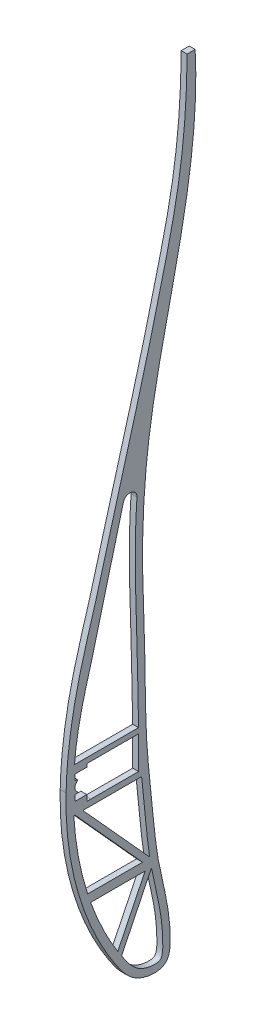
SolidWorks part; units mm, degrees
ref_plane "Front Plane" through (0, 0, 0) normal (0, 0, 1) x (1, 0, 0)
ref_plane "Top Plane" through (0, 0, 0) normal (0, 1, 0) x (1, 0, 0)
ref_plane "Right Plane" through (0, 0, 0) normal (1, 0, 0) x (0, 0, -1)
sketch "rib1" plane through (0, 0, 0) normal (1, 0, 0) x (0, 0, -1)
  line L0 (-71.2313, 530.3957) -> (928.7687, 530.3957) construction
  line L1 (884.1904, 599.9039) -> (887.9745, 599.9039)
  line L2 (856.9345, 370.6416) -> (865.0745, 370.6416)
  line L3 (850.4345, 376.6416) -> (850.4345, 379.6416)
  line L4 (850.4345, 376.6416) -> (850.4345, 373.6416)
  line L5 (840.8063, 376.6416) -> (845.8063, 376.6416) construction
  line L8 (855.8579, 382.6416) -> (843.7452, 382.6416)
  line L9 (855.8579, 382.6416) -> (864.8136, 382.6416)
  line L10 (856.9345, 368.6416) -> (844.7619, 368.6416)
  line L11 (856.9345, 368.6416) -> (865.1127, 368.6416)
  line L12 (866.2204, 340.1291) -> (848.917, 340.1291)
  line L13 (858.3122, 320.8088) -> (858.0269, 320.2668)
  line L14 (848.4203, 343.1291) -> (847.9481, 343.1291)
  line L15 (860.5104, 442.9155) -> (866.5886, 442.9155)
  line L16 (858.0269, 320.2668) -> (873.8862, 320.2668)
  line L17 (855.8579, 318.9992) -> (874.2194, 327.9134) construction
  line L18 (854.766, 321.2482) -> (871.1797, 329.2167) construction
  line L19 (871.1797, 329.2167) -> (873.8862, 320.2668)
  line L20 (843.5049, 367.0528) -> (865.4106, 343.1291)
  line L21 (866.2204, 340.1291) -> (856.8415, 322.3087)
  line L22 (844.7619, 368.6416) -> (867.7752, 343.5082)
  line L23 (868.4574, 340.0851) -> (858.3122, 320.8088)
  line L24 (865.4106, 343.1291) -> (848.4203, 343.1291)
  line L26 (856.9345, 370.6416) -> (850.4345, 370.6416)
  line L27 (850.4345, 370.6416) -> (850.4345, 373.6416)
  line L29 (855.8579, 380.6416) -> (864.9113, 380.6416)
  line L30 (855.8579, 380.6416) -> (850.4345, 380.6416)
  line L31 (850.4345, 380.6416) -> (850.4345, 379.6416)
  circle A0 centre (845.8063, 376.6416) radius 2
  arc A1 (841.0443, 380.5713) -> (847.6718, 415.72) centre (1017.3451, 365.528) cw
  arc A2 (851.2954, 425.5507) -> (861.6081, 456.6454) centre (699.0135, 493.3134) ccw
  arc A3 (862.9829, 461.9026) -> (884.1904, 599.9039) centre (374.0528, 607.6697) ccw
  arc A4 (840.7788, 371.8072) -> (855.8579, 318.9992) centre (950.1899, 374.4922) ccw
  arc A5 (867.6216, 376.9662) -> (872.8022, 332.64) centre (1022.9399, 372.6533) ccw
  arc A6 (867.6216, 376.9662) -> (871.4996, 461.3529) centre (1263.0251, 401.0778) cw
  arc A7 (871.9368, 463.9152) -> (887.9745, 599.9039) centre (-120.6116, 649.9108) ccw
  arc A8 (874.2194, 327.9134) -> (872.8022, 332.64) centre (950.104, 353.2418) cw
  arc A9 (841.0443, 380.5713) -> (840.7788, 371.8072) centre (920.7547, 373.7698) ccw
  arc A10 (851.2954, 425.5507) -> (847.6718, 415.72) centre (924.3857, 393.0268) ccw
  arc A11 (862.9829, 461.9026) -> (861.6081, 456.6454) centre (939.6482, 439.046) ccw
  arc A12 (871.4996, 461.3529) -> (871.9368, 463.9152) centre (950.5681, 449.1804) cw
  arc A13 (843.7452, 382.6416) -> (850.0691, 415.0108) centre (1017.3451, 365.528) cw
  arc A14 (853.5794, 424.5344) -> (850.0691, 415.0108) centre (924.3857, 393.0268) ccw
  arc A15 (853.5794, 424.5344) -> (860.5104, 442.9155) centre (699.0135, 493.3134) ccw
  arc A16 (843.5353, 380.3587) -> (850.0691, 415.0108) centre (1017.3451, 365.528) cw construction
  arc A17 (843.5049, 367.0528) -> (847.9481, 343.1291) centre (950.1899, 374.4922) ccw
  arc A18 (865.0721, 374.4641) -> (865.0745, 370.6416) centre (1022.9399, 372.6533) ccw
  arc A19 (864.962, 379.6766) -> (864.9113, 380.6416) centre (1263.0251, 401.0778) cw
  arc A20 (871.1797, 329.2167) -> (870.3865, 331.9962) centre (950.104, 353.2418) cw
  arc A21 (868.4574, 340.0851) -> (870.3865, 331.9962) centre (1022.9399, 372.6533) ccw
  arc A22 (865.3787, 461.1883) -> (886.6901, 599.8658) centre (374.0528, 607.6697) ccw construction
  arc A23 (865.1195, 376.9245) -> (870.3865, 331.9962) centre (1022.9399, 372.6533) ccw construction
  arc A24 (869.4795, 464.3757) -> (885.4776, 600.0277) centre (-120.6116, 649.9108) ccw construction
  arc A25 (843.278, 371.8685) -> (858.0127, 320.2668) centre (950.1899, 374.4922) ccw construction
  arc A26 (853.5794, 424.5344) -> (864.0469, 456.0955) centre (699.0135, 493.3134) ccw construction
  arc A27 (865.3787, 461.1883) -> (864.0469, 456.0955) centre (939.6482, 439.046) ccw construction
  arc A28 (865.1195, 376.9245) -> (869.0287, 461.7333) centre (1263.0251, 401.0778) cw construction
  arc A29 (869.0287, 461.7333) -> (869.4795, 464.3757) centre (950.5681, 449.1804) cw construction
  arc A30 (848.917, 340.1291) -> (856.8415, 322.3087) centre (950.1899, 374.4922) ccw
  arc A31 (865.1127, 368.6416) -> (867.7752, 343.5082) centre (1022.9399, 372.6533) ccw
  arc A32 (864.8136, 382.6416) -> (866.5886, 442.9155) centre (1263.0251, 401.0778) cw
  arc A33 (865.0721, 374.4641) -> (864.962, 379.6766) centre (785.0773, 375.3817) ccw
  spline S0 degree 3 poles (855.8579, 318.9992) (859.3648, 313.0596) (867.0534, 309.8477) (875.8907, 311.5767) (877.0472, 317.8757) (875.7309, 323.2627) (874.9921, 325.5984) (874.2194, 327.9134) knots 0 0 0 0 0.275026 0.518183 0.708506 0.751927 0.952395 0.952395 0.952395 0.952395
  dimension "D2" = 2.5
  dimension "D1" = 1000
sketch "rib2" plane through (0, 0, 0) normal (1, 0, 0) x (0, 0, -1)
  line L0 (-154.4211, 376.6416) -> (49845.5789, 376.6416) construction
  line L1 (-144.1421, 380.6416) -> (49855.8579, 380.6416) construction
  line L2 (-143.0655, 370.6416) -> (49856.9345, 370.6416) construction
  line L3 (782.8933, 343.3859) -> (760.3563, 368.2109)
  line L4 (-143.0655, 368.6416) -> (49856.9345, 368.6416) construction
  line L5 (-144.1421, 382.6416) -> (49855.8579, 382.6416) construction
  line L6 (785.2354, 343.762) -> (762.6647, 368.6416)
  line L7 (764.6298, 343.3859) -> (782.8933, 343.3859)
  line L8 (783.7374, 340.3859) -> (774.2204, 321.3554)
  line L9 (767.5719, 380.6416) -> (767.5719, 370.6416)
  line L10 (767.5719, 370.6416) -> (782.7291, 370.6416)
  line L11 (767.5719, 380.6416) -> (782.2855, 380.6416)
  line L12 (765.5126, 340.3859) -> (783.7374, 340.3859)
  line L13 (762.6647, 368.6416) -> (782.7755, 368.6416)
  line L14 (776.5435, 321.5294) -> (789.8459, 321.5294)
  line L15 (760.7138, 382.6416) -> (782.1585, 382.6416)
  line L16 (770.7866, 427.4918) -> (781.8144, 427.4918)
  line L17 (801.9062, 590.4081) -> (805.115, 590.4081)
  line L18 (757.9166, 376.6416) -> (762.9166, 376.6416) construction
  line L20 (785.9296, 340.298) -> (776.5435, 321.5294)
  circle A0 centre (762.9166, 376.6416) radius 2
  arc A1 (758.9972, 388.4269) -> (758.7602, 360.0657) centre (857.8646, 373.419) ccw
  spline S0 degree 3 poles (758.7602, 360.0657) (759.4545, 354.9126) (761.6392, 342.918) (767.6025, 326.3565) (776.3644, 313.1833) (785.8807, 308.842) (791.3139, 310.6103) (793.0754, 312.9879) (793.3375, 316.1077) (791.0414, 329.6431) (787.956, 341.1966) (785.2042, 359.6207) (785.4538, 372.9971) (783.4315, 397.4301) (785.2476, 420.7625) (783.0535, 455.8097) (784.4694, 464.3867) (788.1328, 479.2935) (793.2428, 503.9805) (802.5401, 542.6054) (805.2587, 572.3941) (805.115, 590.4081) knots 0.028705 0.028705 0.028705 0.028705 0.059247 0.100348 0.1322 0.149146 0.158796 0.160734 0.16766 0.175847 0.234409 0.24607 0.285136 0.310616 0.385264 0.441942 0.454033 0.506165 0.624061 0.777474 1 1 1 1
  spline S1 degree 3 poles (801.9062, 590.4081) (801.6966, 560.1521) (794.9988, 516.4373) (781.9369, 464.9221) (769.955, 434.3358) (762.9603, 410.299) (759.9193, 394.5015) (758.9972, 388.4269) knots 0 0 0 0 0.408823 0.598513 0.719262 0.854061 0.937351 0.937351 0.937351 0.937351
  spline S2 degree 3 poles (760.3563, 368.2109) (760.6455, 365.1083) (761.2971, 359.3998) (762.6856, 351.2079) (763.8909, 346.0643) (764.604, 343.4789) (764.6298, 343.3859) knots 0.01313 0.01313 0.01313 0.01313 0.031626 0.047245 0.062864 0.063447 0.063447 0.063447 0.063447
  spline S3 degree 3 poles (765.5126, 340.3859) (765.9421, 339.0082) (767.2255, 335.1967) (769.2617, 330.2911) (771.6089, 325.6402) (773.0967, 323.06) (774.0043, 321.6748) (774.2204, 321.3554) knots 0.069751 0.069751 0.069751 0.069751 0.078483 0.094102 0.101912 0.109721 0.112105 0.112105 0.112105 0.112105
  spline S5 degree 3 poles (782.7291, 370.6416) (782.7064, 371.5634) (782.6438, 373.8426) (782.4996, 377.1608) (782.3523, 379.5799) (782.2855, 380.6416) knots 0.276245 0.276245 0.276245 0.276245 0.281529 0.289339 0.295445 0.295445 0.295445 0.295445
  spline S6 degree 3 poles (789.8459, 321.5294) (789.8142, 321.6995) (789.7504, 322.0389) (789.4577, 323.5807) (788.9295, 326.2404) (788.1496, 329.9526) (787.3325, 333.724) (786.5882, 337.1579) (786.1256, 339.3494) (785.9296, 340.298) knots 0.178918 0.178918 0.178918 0.178918 0.179894 0.18087 0.187816 0.195625 0.203435 0.211244 0.21717 0.21717 0.21717 0.21717
  spline S7 degree 3 poles (785.2354, 343.762) (784.9117, 345.4358) (784.3695, 348.4126) (783.6834, 352.846) (783.0923, 358.3507) (782.8866, 363.6197) (782.8011, 367.501) (782.7755, 368.6416) knots 0.224345 0.224345 0.224345 0.224345 0.234672 0.242482 0.250291 0.26591 0.27243 0.27243 0.27243 0.27243
  spline S8 degree 3 poles (782.1585, 382.6416) (782.0098, 384.985) (781.5323, 392.7288) (781.6016, 402.5045) (781.8121, 413.0284) (781.8895, 420.0466) (781.8563, 425.0079) (781.8229, 427.0307) (781.8144, 427.4918) knots 0.299279 0.299279 0.299279 0.299279 0.312767 0.344005 0.359624 0.375243 0.383052 0.385336 0.385336 0.385336 0.385336
  spline S9 degree 3 poles (770.7866, 427.4918) (769.4671, 423.3387) (766.9647, 414.7701) (763.3804, 399.8515) (761.5251, 389.0141) (760.7138, 382.6416) knots 0.752168 0.752168 0.752168 0.752168 0.811773 0.874217 0.962264 0.962264 0.962264 0.962264
  point P26 (765.5126, 340.3859)
  point P30 (764.6298, 343.3859)
  point P35 (774.2204, 321.3554)
  point P36 (789.8459, 321.5294)
  point P37 (785.9296, 340.298)
  point P39 (760.3563, 368.2109)
  point P40 (760.0729, 371.4986)
  dimension "D1" = 100
sketch "Sketch5" plane through (0, 0, 0) normal (1, 0, 0) x (0, 0, -1)
  line L0 (-200154.4211, 376.6416) -> (249845.5789, 376.6416) construction
  line L1 (693.317, 322.1015) -> (707.0464, 322.1015)
  line L2 (695.5696, 447.1101) -> (698.3736, 447.1101)
  line L3 (698.6642, 410.7316) -> (681.8197, 410.7316)
  line L4 (698.7261, 405.5878) -> (680.4847, 405.5878)
  line L5 (677.0801, 382.6416) -> (699.3215, 382.6416)
  line L7 (699.7026, 368.6416) -> (679.4803, 368.6416)
  line L8 (-200143.0655, 368.6416) -> (249856.9345, 368.6416) construction
  line L9 (674.1545, 376.6416) -> (679.1545, 376.6416) construction
  line L10 (684.2181, 380.6416) -> (684.2181, 370.6416)
  line L11 (-200144.1421, 380.6416) -> (249855.8579, 380.6416) construction
  line L12 (-200143.0655, 370.6416) -> (249856.9345, 370.6416) construction
  line L13 (684.2181, 370.6416) -> (699.6248, 370.6416)
  line L14 (702.2048, 368.6416) -> (702.335, 365.9116)
  line L15 (699.3639, 380.6416) -> (684.2181, 380.6416)
  line L16 (708.485, 312.754) -> (708.6651, 312.9152)
  line L17 (706.7921, 314.6987) -> (706.9599, 314.7434)
  line L18 (699.8434, 365.7077) -> (699.7071, 368.5354)
  line L19 (682.1263, 343.4207) -> (681.5591, 343.4207)
  line L20 (700.6109, 340.4181) -> (682.6985, 340.4181)
  line L21 (699.3639, 380.6416) -> (699.6248, 370.6416)
  line L22 (705.0572, 343.4207) -> (704.8181, 343.4207)
  line L23 (716.7384, 582.0418) -> (720.2752, 582.0418)
  line L24 (693.317, 322.1015) -> (702.7962, 340.2834)
  line L25 (702.2445, 343.7103) -> (679.4803, 368.6416)
  line L26 (691.5466, 323.0319) -> (700.6109, 340.4181)
  line L28 (699.8006, 343.4207) -> (682.1263, 343.4207)
  line L32 (699.8006, 343.4207) -> (677.0187, 368.3713)
  circle A0 centre (679.1545, 376.6416) radius 2
  spline S0 degree 3 poles (674.1545, 376.6416) (674.6209, 363.9047) (675.4244, 348.9718) (687.0005, 324.6734) (691.715, 318.3055) (697.5054, 311.9056) (699.9912, 310.5046) (704.8962, 310.5781) (707.1739, 311.6254) (708.485, 312.754) knots 0 0 0 0 0.082297 0.137777 0.177735 0.177735 0.194632 0.194632 0.2043 0.2043 0.2043 0.2043
  spline S1 degree 3 poles (716.7384, 582.0418) (716.9491, 569.6586) (716.384, 531.2528) (699.2016, 484.7456) (692.8166, 441.1757) (677.838, 413.403) (675.0171, 391.1698) (674.1545, 376.6416) knots 0 0 0 0 0.169562 0.555938 0.689283 0.791056 1 1 1 1
  spline S2 degree 3 poles (702.2445, 343.7103) (702.1641, 344.2407) (701.7657, 346.9448) (701.1382, 351.8745) (700.5581, 357.5193) (700.1402, 362.1447) (699.9401, 364.5255) (699.8434, 365.7077) knots 0.317112 0.317112 0.317112 0.317112 0.32289 0.346516 0.370142 0.381955 0.393768 0.393768 0.393768 0.393768
  spline S4 degree 3 poles (702.2048, 368.6416) (701.8669, 376.5926) (701.8555, 384.7425) (701.1266, 402.784) (701.1396, 431.7405) (700.5544, 456.9254) (705.1133, 487.005) (717.5576, 525.1697) (721.078, 562.1394) (720.2752, 582.0418) knots 0.402967 0.402967 0.402967 0.402967 0.483086 0.483086 0.591391 0.687653 0.687653 0.844633 1 1 1 1
  spline S5 degree 3 poles (699.3215, 382.6416) (699.3024, 383.5334) (699.2425, 386.2646) (699.1476, 389.8671) (699.0014, 393.4021) (698.878, 397.2735) (698.7899, 401.3622) (698.7401, 404.5905) (698.7261, 405.5878) knots 0.449941 0.449941 0.449941 0.449941 0.458939 0.477596 0.486925 0.496254 0.514911 0.523067 0.523067 0.523067 0.523067
  spline S6 degree 3 poles (699.7071, 368.5354) (699.7056, 368.5708) (699.7041, 368.6062) (699.7026, 368.6416) knots 0.402967 0.402967 0.402967 0.402967 0.40332 0.40332 0.40332 0.40332
  spline S7 degree 3 poles (682.6985, 340.4181) (683.0121, 339.6321) (683.9949, 337.2558) (685.7648, 333.3639) (687.9735, 329.011) (689.7493, 325.8616) (690.8989, 324.0094) (691.3927, 323.2607) (691.5466, 323.0319) knots 0.095831 0.095831 0.095831 0.095831 0.10215 0.114919 0.127687 0.140456 0.14684 0.149678 0.149678 0.149678 0.149678
  spline S8 degree 3 poles (677.0187, 368.3713) (677.0192, 368.3626) (677.0681, 367.4934) (677.2257, 364.9551) (677.5669, 360.9606) (678.1637, 356.4034) (679.0103, 351.9539) (680.1158, 347.6804) (681.0683, 344.7879) (681.5591, 343.4207) knots 0.019088 0.019088 0.019088 0.019088 0.019153 0.025537 0.038306 0.051075 0.063844 0.076612 0.087747 0.087747 0.087747 0.087747
  spline S9 degree 3 poles (708.6651, 312.9152) (709.0596, 313.2832) (711.3268, 316.9807) (705.4793, 334.2076) (703.6294, 350.0939) (702.335, 365.9116) knots 0.204759 0.204759 0.204759 0.204759 0.207895 0.236848 0.393768 0.393768 0.393768 0.393768
  spline S10 degree 3 poles (676.659, 376.6416) (676.6584, 376.6321) (676.6578, 376.6225) (676.6573, 376.613) knots 0.999862 0.999862 0.999862 0.999862 1 1 1 1
  spline S11 degree 3 poles (707.0464, 322.1015) (707.0052, 322.2371) (706.9227, 322.5094) (706.5342, 323.8003) (705.9077, 326.017) (705.0863, 329.1749) (704.0811, 333.4582) (703.3421, 337.155) (702.8797, 339.7948) (702.7962, 340.2834) knots 0.237993 0.237993 0.237993 0.237993 0.239469 0.240946 0.252011 0.263824 0.275637 0.299263 0.304623 0.304623 0.304623 0.304623
  spline S12 degree 3 poles (680.4847, 405.5878) (680.2388, 404.5378) (679.0822, 399.2686) (677.9122, 391.5905) (677.2696, 384.9533) (677.0801, 382.6416) knots 0.859357 0.859357 0.859357 0.859357 0.875 0.9375 0.970921 0.970921 0.970921 0.970921
  spline S13 degree 3 poles (698.6642, 410.7316) (698.6438, 412.7052) (698.5832, 419.5769) (698.503, 431.741) (698.3426, 441.7088) (698.3711, 446.7739) (698.3736, 447.1101) knots 0.536769 0.536769 0.536769 0.536769 0.552225 0.58954 0.626855 0.629511 0.629511 0.629511 0.629511
  spline S15 degree 3 poles (695.5696, 447.1101) (695.4451, 446.6155) (694.7557, 443.952) (693.3092, 439.1408) (690.7575, 432.8707) (687.9819, 426.8359) (685.294, 420.8884) (683.2818, 415.5566) (682.219, 412.126) (681.8197, 410.7316) knots 0.649129 0.649129 0.649129 0.649129 0.65625 0.6875 0.71875 0.75 0.78125 0.8125 0.833615 0.833615 0.833615 0.833615
sketch "Sketch6" plane through (0, 0, 0) normal (1, 0, 0) x (0, 0, -1)
  line L0 (-200154.4211, 376.6416) -> (249845.5789, 376.6416) construction
  line L3 (617.0002, 368.6416) -> (597.1315, 368.6416)
  line L4 (-200143.0655, 368.6416) -> (249856.9345, 368.6416) construction
  line L5 (635.098, 572.5915) -> (632.0869, 572.5915)
  line L6 (615.9917, 380.6416) -> (615.9917, 381.6944)
  line L7 (609.0006, 321.5886) -> (608.931, 321.4458)
  line L8 (610.7981, 320.7115) -> (610.2002, 319.4863)
  line L9 (594.4326, 368.6416) -> (594.0581, 368.6416)
  line L10 (591.4519, 376.6416) -> (596.4519, 376.6416) construction
  line L11 (594.4326, 368.6416) -> (617.3118, 343.3906)
  line L12 (618.1756, 340.3906) -> (609.0006, 321.5886)
  line L13 (597.1315, 368.6416) -> (619.7239, 343.7071)
  line L14 (594.4519, 376.6416) -> (594.4519, 374.6416) construction
  line L15 (594.4519, 374.6416) -> (594.4519, 372.6416)
  line L16 (594.4519, 372.6416) -> (598.4519, 372.6416)
  line L17 (598.4519, 380.6416) -> (598.4519, 381.6944)
  line L18 (594.4519, 374.6416) -> (595.187, 374.6416)
  line L19 (594.4519, 378.6416) -> (594.4519, 380.6416)
  line L20 (594.4519, 380.6416) -> (598.4519, 380.6416)
  line L21 (594.4519, 378.6416) -> (595.187, 378.6416)
  line L22 (598.4519, 381.6944) -> (599.7563, 381.6944)
  line L23 (620.3211, 340.2268) -> (610.7981, 320.7115)
  line L24 (599.7563, 381.6944) -> (599.7401, 381.7251)
  line L25 (615.9602, 383.484) -> (594.2761, 383.484)
  line L26 (598.4519, 372.6416) -> (598.4519, 370.6433)
  line L27 (615.9917, 370.6132) -> (599.7563, 370.6433)
  line L28 (618.1756, 340.3906) -> (599.7563, 340.3906)
  line L29 (617.3118, 343.3906) -> (598.7382, 343.3906)
  line L30 (598.4519, 370.6433) -> (599.7563, 370.6433)
  line L35 (599.7563, 381.6944) -> (615.9917, 381.6944)
  line L36 (615.9917, 380.6416) -> (615.9917, 370.6132)
  arc A0 (610.8725, 452.2517) -> (615.4146, 451.3048) centre (613.0575, 451.3657) cw
  arc A1 (595.302, 378.2779) -> (595.302, 375.0052) centre (596.4519, 376.6416) ccw
  arc A2 (595.187, 378.6416) -> (595.302, 378.2779) centre (595.187, 378.4416) cw
  arc A3 (595.302, 375.0052) -> (595.187, 374.6416) centre (595.187, 374.8416) cw
  spline S0 degree 3 poles (591.4519, 376.6416) (590.8724, 355.6832) (598.0127, 330.747) (614.7237, 309.0913) (626.4002, 308.0944) (627.1878, 324.0074) (622.1741, 339.2467) (620.5135, 359.7877) (618.195, 380.0068) (618.3402, 403.8303) (616.7499, 433.3564) (618.9592, 474.5213) (631.6465, 520.1908) (636.0177, 556.3417) (635.098, 572.5915) knots 0 0 0 0 0.181753 0.211103 0.236632 0.255743 0.327686 0.385848 0.430346 0.504499 0.591378 0.686471 0.859586 1 1 1 1
  spline S1 degree 3 poles (632.3767, 572.5915) (632.331, 559.797) (630.7518, 538.4728) (623.6454, 509.5847) (617.1086, 483.6159) (609.1878, 456.4292) (602.6277, 431.1093) (594.4581, 405.0022) (591.6906, 387.7261) (591.4519, 376.6416) knots 0 0 0 0 0.191351 0.317516 0.443871 0.591483 0.740453 0.834547 1 1 1 1
  spline S2 degree 3 poles (619.7239, 343.7071) (619.5881, 344.5842) (619.2022, 347.2732) (618.6764, 351.7986) (618.1443, 357.2765) (617.6179, 362.6875) (617.2186, 366.4692) (617.0187, 368.4566) (617.0002, 368.6416) knots 0.33611 0.33611 0.33611 0.33611 0.343735 0.359361 0.374986 0.390612 0.406237 0.40784 0.40784 0.40784 0.40784
  spline S3 degree 3 poles (599.7563, 340.3906) (599.7882, 340.3011) (600.4188, 338.5434) (601.7436, 335.154) (603.9399, 330.3213) (606.3333, 325.742) (608.0626, 322.8243) (608.931, 321.4458) knots 0.108518 0.108518 0.108518 0.108518 0.109355 0.124981 0.140606 0.156231 0.170688 0.170688 0.170688 0.170688
  spline S4 degree 3 poles (610.8725, 452.2517) (610.269, 449.893) (608.8998, 444.6758) (606.7371, 436.6294) (604.5222, 428.0779) (602.3578, 419.4861) (600.0573, 410.8763) (597.5945, 402.3898) (595.6103, 393.891) (594.6577, 387.5489) (594.3266, 384.0736) (594.2761, 383.484) knots 0.448611 0.448611 0.448611 0.448611 0.500019 0.562521 0.625024 0.687526 0.750029 0.812531 0.875033 0.937536 0.950297 0.950297 0.950297 0.950297
  spline S5 degree 3 poles (594.0581, 368.6416) (594.1057, 367.7673) (594.4036, 363.3735) (595.4715, 355.4692) (597.3077, 347.9625) (598.5477, 343.9825) (598.7382, 343.3906) knots 0.023466 0.023466 0.023466 0.023466 0.031229 0.062479 0.09373 0.09921 0.09921 0.09921 0.09921
  spline S6 degree 3 poles (610.2002, 319.4863) (610.3292, 319.2923) (610.9476, 318.3692) (612.075, 316.7416) (613.5938, 314.8775) (615.268, 313.3623) (617.1903, 312.2288) (619.6971, 311.4612) (621.7209, 311.3604) (622.8414, 311.5923) (623.3355, 311.851) (623.4973, 312.0037) (623.7734, 312.4798) (624.0122, 313.3728) (624.1915, 314.9548) (624.1754, 317.4057) (624.0268, 320.2009) (623.7469, 322.9038) (623.3647, 325.5305) (622.9006, 328.1059) (622.2032, 331.5008) (621.2956, 335.4836) (620.6086, 338.7108) (620.3211, 340.2268) knots 0.177597 0.177597 0.177597 0.177597 0.179669 0.187482 0.195295 0.203107 0.21092 0.218733 0.226545 0.230452 0.234358 0.238264 0.242171 0.246077 0.249983 0.257796 0.265609 0.273421 0.281234 0.289047 0.296859 0.312485 0.325931 0.325931 0.325931 0.325931
  spline S7 degree 3 poles (615.9602, 383.484) (615.8839, 385.6186) (615.7479, 391.3851) (615.6642, 400.7347) (615.3415, 411.5075) (614.9499, 422.3472) (614.7472, 433.2494) (614.9316, 442.9184) (615.2536, 448.9371) (615.4146, 451.3048) knots 0.450406 0.450406 0.450406 0.450406 0.468738 0.499989 0.53124 0.56249 0.593741 0.624992 0.645293 0.645293 0.645293 0.645293
  point P52 (594.4519, 374.6416)
  dimension "D1" = 0.2
  dimension "D2" = 0.2
extrude "Boss-Extrude6" add sketch "Sketch6" along normal blind 2
equation "\"1000mmm\"=767.321"
